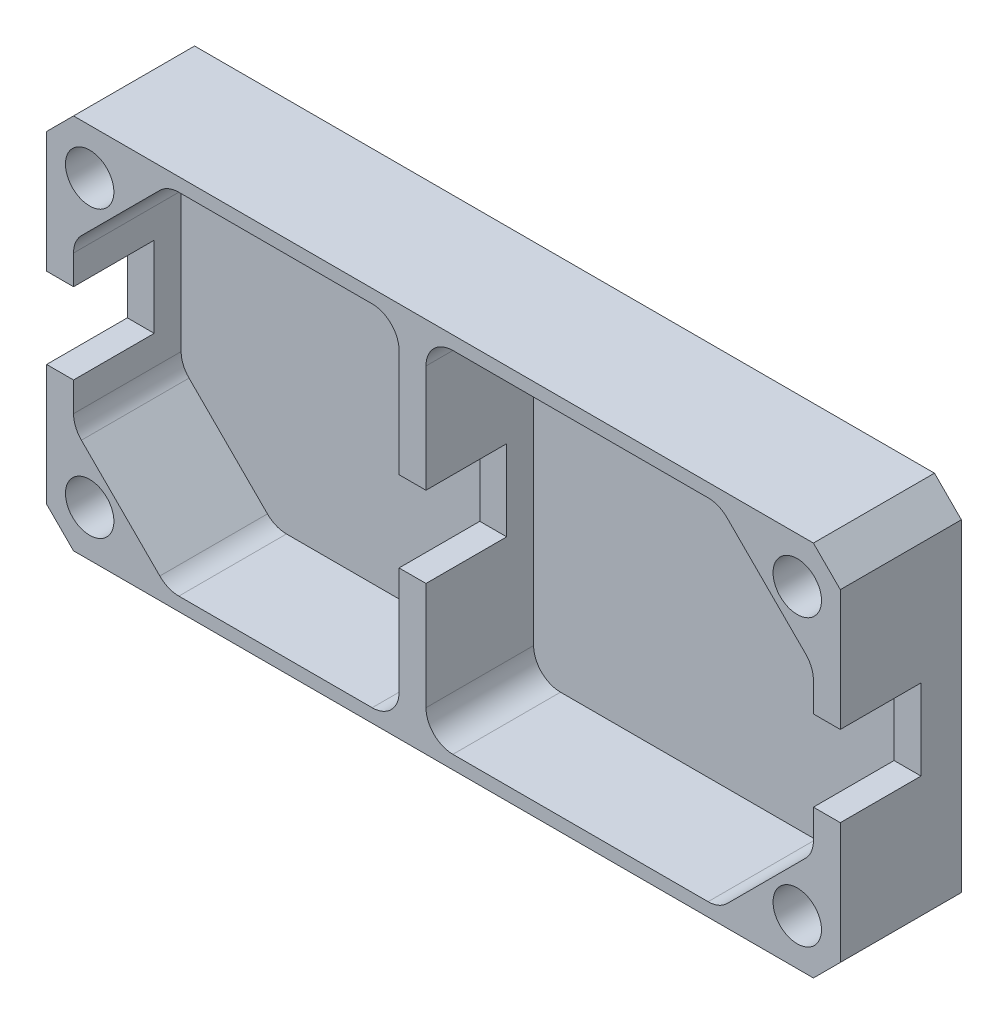
SolidWorks part; units mm, degrees
material "Д16Т ГОСТ 4784-74"
ref_plane "Спереди" through (0, 0, 0) normal (0, 0, 1) x (1, 0, 0)
ref_plane "Сверху" through (0, 0, 0) normal (0, 1, 0) x (1, 0, 0)
ref_plane "Справа" through (0, 0, 0) normal (1, 0, 0) x (0, 0, -1)
sketch "Эскиз1" plane through (0, 0, 0) normal (0, 0, 1) x (1, 0, 0)
  line L5 (-14.75, 7) -> (14.75, 7)
  line L6 (-14.75, 7) -> (-14.75, -7)
  line L7 (-14.75, -7) -> (14.75, -7)
  line L8 (14.75, 7) -> (14.75, -7)
  line L9 (-14.75, 7) -> (14.75, -7) construction
  line L10 (-14.75, -7) -> (14.75, 7) construction
  point P0 (0, 0)
  dimension "D1" = 29.5
  dimension "D2" = 14
extrude "Бобышка-Вытянуть1" add sketch "Эскиз1" along normal blind 4.5
sketch "Эскиз2" plane through (0, 0, 4.5) normal (0, 0, 1) x (1, 0, 0)
  line L0 (-14.75, 7) -> (-14.75, -7) construction
  line L1 (-10.25, 6.5) -> (-1.65, 6.5)
  line L2 (-13.75, 3) -> (-13.75, -3)
  line L3 (-10.25, -6.5) -> (-1.65, -6.5)
  line L4 (-1.65, 6.5) -> (-1.65, -6.5)
  line L5 (14.75, 7) -> (-14.75, 7) construction
  line L6 (-14.75, -7) -> (14.75, -7) construction
  line L7 (-13.75, 3) -> (-10.25, 6.5)
  line L13 (-13.75, -3) -> (-10.25, -6.5)
  line L17 (-1.15, -3.4468) -> (-1.15, 2.0835) construction
  line L18 (-0.65, 6.5) -> (10.25, 6.5)
  line L19 (-0.65, 6.5) -> (-0.65, -6.5)
  line L20 (-0.65, -6.5) -> (10.25, -6.5)
  line L21 (13.75, 3) -> (13.75, -3)
  line L22 (14.75, -7) -> (14.75, 7) construction
  line L23 (10.25, 6.5) -> (13.75, 3)
  line L24 (10.25, -6.5) -> (13.75, -3)
  line L26 (-14.75, 7) -> (-14.75, -7) construction
  point P0 (-13.75, 6.5)
  point P2 (-13.75, -6.5)
  point P21 (13.75, -6.5)
  point P24 (13.75, 6.5)
  dimension "D1" = 1
  dimension "D2" = 0.5
  dimension "D3" = 0.5
  dimension "D4" = 13.6
  dimension "D5" = 1
  dimension "D9" = 1
extrude "Вырез-Вытянуть1" cut sketch "Эскиз2" against normal offset from surface (4 mm away) 0.5 up to face at (0, 0, 0)
chamfer "Фаска1" distance 1 angle 45 4 edges at (-14.75, -7, 2.25) (-14.75, 7, 2.25) (14.75, -7, 2.25) (14.75, 7, 2.25)
hole_wizard "Отверстие с зазором M1,61" positions "Эскиз3" profile "Эскиз4" hole size "M1,6" standard "GOST"
sketch "Эскиз3" plane through (0, 0, 4.5) normal (0, 0, 1) x (1, 0, 0)
  line L3 (0, 0) -> (-4.9499, 0) construction
  line L4 (0, 0) -> (0, 3.1635) construction
  point P0 (-13.15, 5.3)
  point P7 (13.15, 5.3)
  point P11 (-13.15, -5.3)
  point P13 (13.15, -5.3)
  dimension "D1" = 10.6
  dimension "D2" = 26.3
sketch "Эскиз4" plane through (-13.15, 5.3, 4.5) normal (1, 0, 0) x (0, -1, 0)
  line L0 (0, 0) -> (0, 14.5408)
  line L1 (0, 14.5408) -> (0.9, 14)
  line L2 (0.9, 14) -> (0.9, 0)
  line L5 (0.9, 0) -> (0, 0)
  line L10 (0, 14.5408) -> (-0.9, 14) construction
  line L11 (0, -6.35) -> (0, 107.95) construction
  dimension "Диаметр отверстия" = 1.8
  dimension "Глубина отверстия" = 14
  dimension "Угол заточки сверла" = 118
fillet "Скругление1" radius 1 12 edges at (10.25, 6.5, 2.5) (13.75, 3, 2.5) (13.75, -3, 2.5) (10.25, -6.5, 2.5) (-0.65, -6.5, 2.5) (-10.25, 6.5, 2.5) (-1.65, 6.5, 2.5) (-1.65, -6.5, 2.5) (-10.25, -6.5, 2.5) (-13.75, -3, 2.5) (-13.75, 3, 2.5) (-0.65, 6.5, 2.5)
sketch "Эскиз5" plane through (0, 0, 4.5) normal (0, 0, 1) x (1, 0, 0)
  line L0 (14.75, -6) -> (14.75, 6) construction
  line L1 (-14.75, 1.5) -> (14.75, 1.5)
  line L2 (-14.75, 1.5) -> (-14.75, -1.5)
  line L3 (-14.75, -1.5) -> (14.75, -1.5)
  line L4 (14.75, 1.5) -> (14.75, -1.5)
  line L5 (-14.75, 1.5) -> (14.75, -1.5) construction
  line L6 (-14.75, -1.5) -> (14.75, 1.5) construction
  point P0 (0, 0)
  dimension "D1" = 3
extrude "Вырез-Вытянуть2" cut sketch "Эскиз5" against normal blind 3
chamfer "Фаска2" distance 0.6 angle 45 4 edges at (-12.25, 5.3, 0) (-12.25, -5.3, 0) (14.05, -5.3, 0) (14.05, 5.3, 0)
sketch "Эскиз6" plane through (0, 0, 0) normal (0, 0, -1) x (-1, 0, 0)
  line L0 (-13.25, 0) -> (-9.75, 0.6171)
  line L1 (-9.75, 0.6171) -> (-9.75, -0.6171)
  line L2 (-9.75, -0.6171) -> (-13.25, 0)
  line L3 (0, 0) -> (-13.25, 0) construction
  line L5 (-14.75, -6) -> (-14.75, 6) construction
  dimension "D1" = 5
  dimension "D2" = 3.5
  dimension "D3" = 20
extrude "Вырез-Вытянуть3" cut sketch "Эскиз6" against normal blind 0.01
